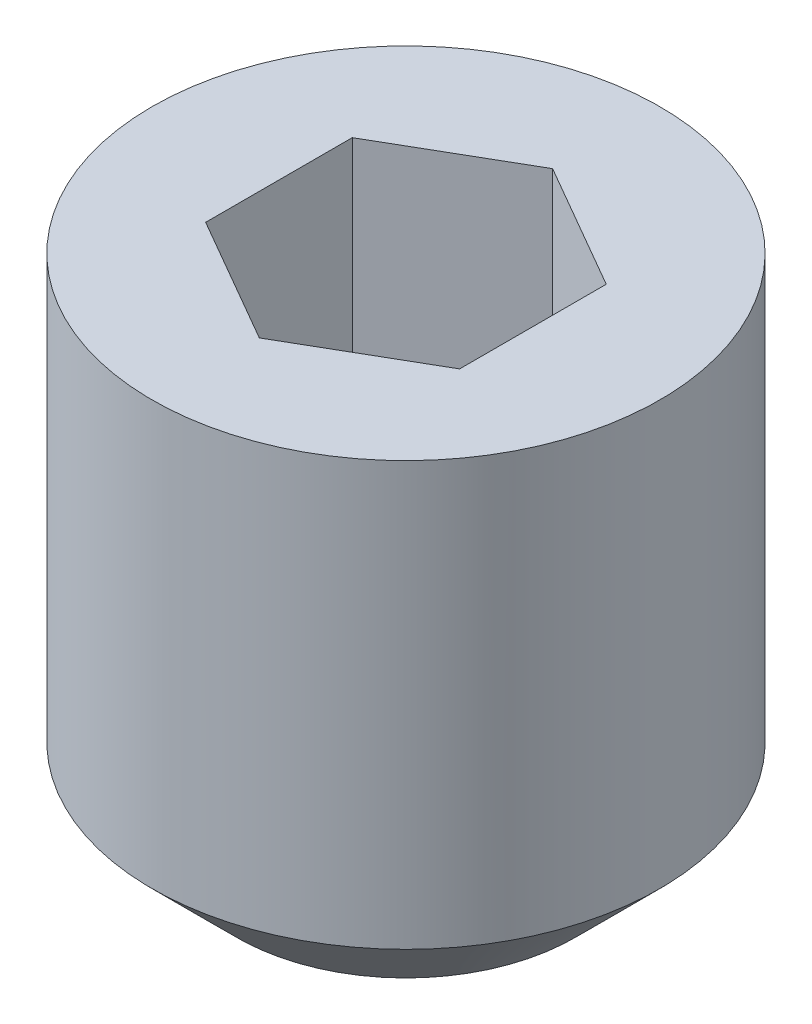
SolidWorks part; units mm, degrees
ref_plane "Front Plane" through (0, 0, 0) normal (0, 0, 1) x (1, 0, 0)
ref_plane "Top Plane" through (0, 0, 0) normal (0, 1, 0) x (1, 0, 0)
ref_plane "Right Plane" through (0, 0, 0) normal (1, 0, 0) x (0, 0, -1)
sketch "Sketch1" plane through (0, 0, 0) normal (0, 0, 1) x (1, 0, 0)
  line L0 (0, 3) -> (0, 0) construction
  line L1 (0, 3) -> (1.5, 3)
  line L2 (1.5, 3) -> (1.5, 0)
  line L3 (1.5, 0) -> (0, 0)
  line L4 (0, 3) -> (0, 0)
  dimension "SS_M" = 3
  dimension "SS_L" = 3
revolve "Revolve1" add sketch "Sketch1" angle 360 about L0
cosmetic thread "Cosmetic Thread1" parameters "SS_D1_s"=2.459
sketch "Sketch2" plane through (0, 0, 0) normal (0, 0, 1) x (1, 0, 0)
  line L0 (0, 3) -> (0, 1.367) construction
  line L1 (0, 3) -> (0.75, 3)
  line L2 (0.75, 3) -> (0.75, 1.8)
  line L3 (0.75, 1.8) -> (0, 1.367)
  line L4 (0, 3) -> (0, 1.367)
  line L5 (1.5, 3) -> (-1.5, 3) construction
  dimension "D3" = 60
  dimension "SS_C" = 1.2
  dimension "SS_B" = 1.5
revolve "Cut-Revolve1" cut sketch "Sketch2" angle 360 about L0
sketch "Sketch3" plane through (0, 3, 0) normal (0, 1, 0) x (1, 0, 0)
  line L1 (0, 0.866) -> (-0.75, 0.433)
  line L2 (-0.75, 0.433) -> (-0.75, -0.433)
  line L3 (-0.75, -0.433) -> (0, -0.866)
  line L4 (0, -0.866) -> (0.75, -0.433)
  line L5 (0.75, -0.433) -> (0.75, 0.433)
  line L6 (0.75, 0.433) -> (0, 0.866)
  circle A0 centre (0, 0) radius 0.75 construction
  circle A1 centre (0, 0) radius 0.75 construction
extrude "Cut-Extrude1" cut sketch "Sketch3" against normal blind 1.2
sketch "Sketch4" plane through (0, 0, 0) normal (0, 0, 1) x (1, 0, 0)
  line L0 (1, 0) -> (1.5, 0)
  line L1 (1.5, 0) -> (1.5, 0.5)
  line L2 (1.5, 0.5) -> (1, 0)
  line L4 (-1.5, 0) -> (1.5, 0) construction
  line L5 (0, 0) -> (0, 3) construction
  line L6 (1.5, 3) -> (-1.5, 3) construction
  line L7 (1.5, 3) -> (1.5, 0) construction
  dimension "D1" = 45
  dimension "SS_D_s" = 2
revolve "Cut-Revolve2" cut sketch "Sketch4" angle 360 about L5
